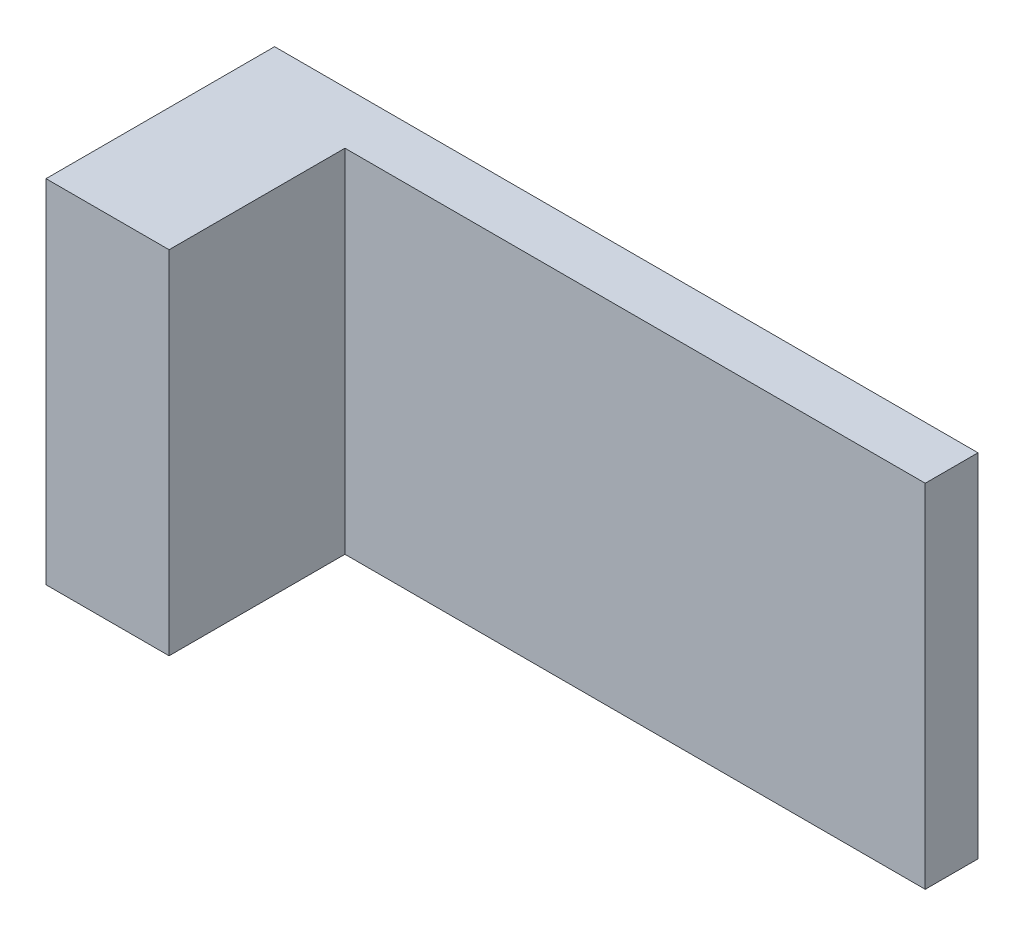
SolidWorks part; units mm, degrees
ref_plane "Front Plane" through (0, 0, 0) normal (0, 0, 1) x (1, 0, 0)
ref_plane "Top Plane" through (0, 0, 0) normal (0, 1, 0) x (1, 0, 0)
ref_plane "Right Plane" through (0, 0, 0) normal (1, 0, 0) x (0, 0, -1)
sketch "Sketch1" plane through (0, 0, 0) normal (0, 0, 1) x (1, 0, 0)
  line L1 (-20, -10) -> (20, -10)
  line L2 (-20, -10) -> (-20, 10)
  line L3 (-20, 10) -> (20, 10)
  line L4 (20, -10) -> (20, 10)
  line L5 (-20, -10) -> (20, 10) construction
  line L6 (-20, 10) -> (20, -10) construction
  point P0 (0, 0)
  dimension "D1" = 40
  dimension "D2" = 20
extrude "Boss-Extrude1" add sketch "Sketch1" along normal mid plane 3
sketch "Sketch2" plane through (0, 0, 1.5) normal (0, 0, 1) x (1, 0, 0)
  line L0 (-20, -10) -> (20, -10) construction
  line L1 (-20, 10) -> (-13, 10)
  line L2 (-20, 10) -> (-20, -10)
  line L3 (-20, -10) -> (-13, -10)
  line L4 (-13, 10) -> (-13, -10)
  dimension "D1" = 7
extrude "Boss-Extrude2" add sketch "Sketch2" along normal blind 10
